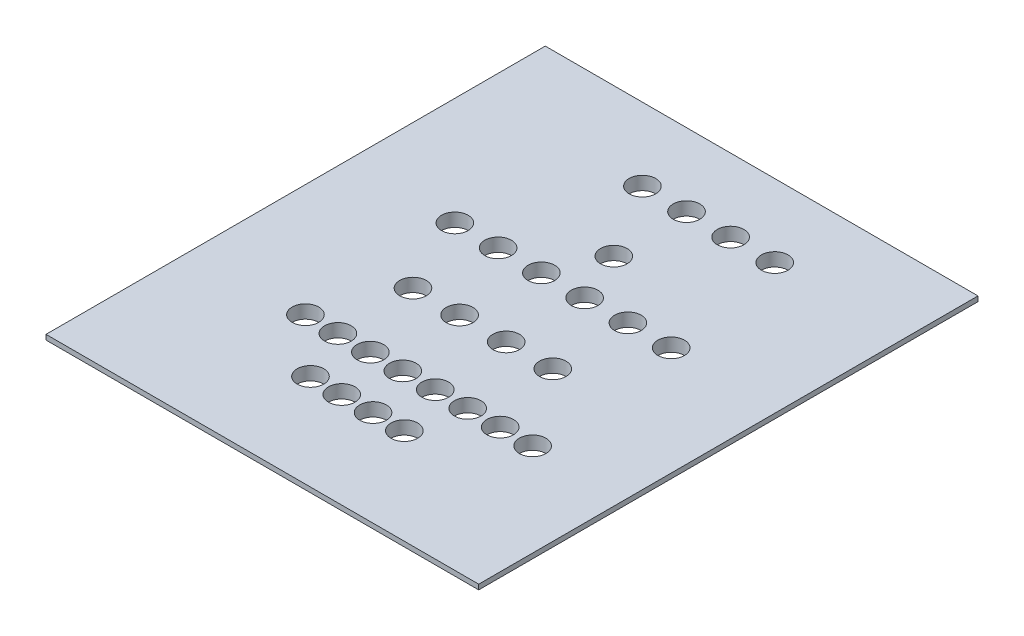
SolidWorks part; units mm, degrees
ref_plane "Спереди" through (0, 0, 0) normal (0, 0, 1) x (1, 0, 0)
ref_plane "Сверху" through (0, 0, 0) normal (0, 1, 0) x (1, 0, 0)
ref_plane "Справа" through (0, 0, 0) normal (1, 0, 0) x (0, 0, -1)
sketch "Эскиз1" plane through (0, 0, 0) normal (0, 1, 0) x (1, 0, 0)
  line L1 (-130, 150) -> (130, 150)
  line L2 (-130, 150) -> (-130, -150)
  line L3 (-130, -150) -> (130, -150)
  line L4 (130, 150) -> (130, -150)
extrude "Бобышка-Вытянуть1" add sketch "Эскиз1" along normal blind 10
sketch "Эскиз2" plane through (0, 0, 0) normal (0, -1, 0) x (1, 0, 0)
  line L1 (110, -130) -> (-110, -130)
  line L2 (110, -130) -> (110, 130)
  line L3 (110, 130) -> (-110, 130)
  line L4 (-110, -130) -> (-110, 130)
  line L5 (110, -130) -> (-110, 130) construction
  line L6 (110, 130) -> (-110, -130) construction
  point P0 (0, 0)
extrude "Вырез-Вытянуть1" cut sketch "Эскиз2" against normal blind 2
sketch "Эскиз3" plane through (0, 0, 0) normal (0, -1, 0) x (1, 0, 0)
  line L0 (171.2544, 0) -> (-164.899, 0) construction
  line L2 (0, -256.8269) -> (0, 255.5523) construction
  point P3 (-115, -185)
  point P4 (115, 185)
  point P8 (-115, 185)
  point P10 (115, -185)
  point P13 (0, -185)
  point P14 (115, 0)
  point P15 (0, 185)
  point P16 (-115, 0)
hole_wizard "Отверстие обработанное метчиком M3x0.51" positions "Эскиз5" profile "Эскиз4" tap size "M3x0.5" standard "Ansi Metric"
sketch "Эскиз5" plane through (0, 0, 0) normal (0, -1, 0) x (-1, 0, 0)
  point P0 (-115, 135)
  point P3 (0, 135)
  point P6 (115, 135)
  point P9 (115, -135)
  point P12 (0, -135)
  point P15 (-115, -135)
  point P28 (-115, 135)
  point P30 (0, 135)
  point P32 (115, 135)
  point P34 (115, 0)
  point P37 (115, -135)
  point P39 (0, -135)
  point P41 (-115, -135)
  point P43 (-115, 0)
sketch "Эскиз4" plane through (115, 0, -135) normal (1, 0, 0) x (0, 0, -1)
  line L0 (0, 0) -> (0, 9.2511)
  line L1 (0, 9.2511) -> (1.25, 8.5)
  line L2 (1.25, 8.5) -> (1.25, 0)
  line L5 (1.25, 0) -> (0, 0)
  line L10 (0, 9.2511) -> (-1.25, 8.5) construction
  line L11 (0, -6.35) -> (0, 107.95) construction
  dimension "Диаметр сверла" = 2.5
  dimension "Глубина сверла" = 8.5
  dimension "Угол заточки сверла" = 118
cosmetic thread "Отверстие резьбы7" parameters "D1"=6, "D2"=3
cosmetic thread "Отверстие резьбы8" parameters "D1"=6, "D2"=3
cosmetic thread "Отверстие резьбы9" parameters "D1"=6, "D2"=3
cosmetic thread "Отверстие резьбы10" parameters "D1"=6, "D2"=3
cosmetic thread "Отверстие резьбы11" parameters "D1"=6, "D2"=3
cosmetic thread "Отверстие резьбы12" parameters "D1"=6, "D2"=3
cosmetic thread "Отверстие резьбы13" parameters "D1"=6, "D2"=3
cosmetic thread "Отверстие резьбы14" parameters "D1"=6, "D2"=3
cosmetic thread "Отверстие резьбы15" parameters "D1"=6, "D2"=3
cosmetic thread "Отверстие резьбы16" parameters "D1"=6, "D2"=3
cosmetic thread "Отверстие резьбы17" parameters "D1"=6, "D2"=3
cosmetic thread "Отверстие резьбы18" parameters "D1"=6, "D2"=3
cosmetic thread "Отверстие резьбы19" parameters "D1"=6, "D2"=3
cosmetic thread "Отверстие резьбы20" parameters "D1"=6, "D2"=3
sketch "Эскиз9" plane through (0, 0, 0) normal (0, -1, 0) x (1, 0, 0)
  line L2 (-130, 150) -> (130, 150)
  line L3 (-130, 150) -> (-130, -150)
  line L4 (-130, -150) -> (130, -150)
  line L5 (130, 150) -> (130, -150)
  line L6 (-130, 150) -> (130, -150) construction
  line L7 (-130, -150) -> (130, 150) construction
  line L8 (-120, 140) -> (120, 140)
  line L9 (-120, 140) -> (-120, -140)
  line L10 (-120, -140) -> (120, -140)
  line L11 (120, 140) -> (120, -140)
  line L12 (-120, 140) -> (120, -140) construction
  line L13 (-120, -140) -> (120, 140) construction
  point P0 (0, 0)
  point P6 (0, 0)
extrude "Вырез-Вытянуть3" cut sketch "Эскиз9" against normal blind 7
sketch "Эскиз10" plane through (0, 10, 0) normal (0, 1, 0) x (1, 0, 0)
  circle A0 centre (74.2212, -61.8295) radius 8
  circle A1 centre (54.7212, -61.8295) radius 8
  circle A2 centre (35.2212, -61.8295) radius 8
  circle A3 centre (15.7212, -61.8295) radius 8
  circle A4 centre (-3.7788, -61.8295) radius 8
  circle A5 centre (-23.2788, -61.8295) radius 8
  circle A6 centre (-42.7788, -61.8295) radius 8
  circle A7 centre (-62.2788, -61.8295) radius 8
  circle A11 centre (27.7567, -92.4433) radius 8
  circle A12 centre (8.9567, -92.4433) radius 8
  circle A13 centre (-9.8433, -92.4433) radius 8
  circle A14 centre (-28.6433, -92.4433) radius 8
  circle A15 centre (40.198, -15.696) radius 8
  circle A16 centre (12.198, -15.696) radius 8
  circle A17 centre (-15.802, -15.696) radius 8
  circle A18 centre (-43.802, -15.696) radius 8
  circle A19 centre (64.8415, 30.8064) radius 8
  circle A20 centre (38.8415, 30.8064) radius 8
  circle A21 centre (12.8415, 30.8064) radius 8
  circle A22 centre (-13.1585, 30.8064) radius 8
  circle A23 centre (-39.1585, 30.8064) radius 8
  circle A24 centre (-65.1585, 30.8064) radius 8
  circle A25 centre (51.5758, 106.2834) radius 8
  circle A26 centre (25.0758, 106.2834) radius 8
  circle A27 centre (-1.4242, 106.2834) radius 8
  circle A28 centre (-27.9242, 106.2834) radius 8
  circle A29 centre (-0.1036, 61.2761) radius 8
  dimension "D3" = 4
  dimension "D4" = 6
  dimension "D5" = 4
extrude "Вырез-Вытянуть4" cut sketch "Эскиз10" against normal through all
